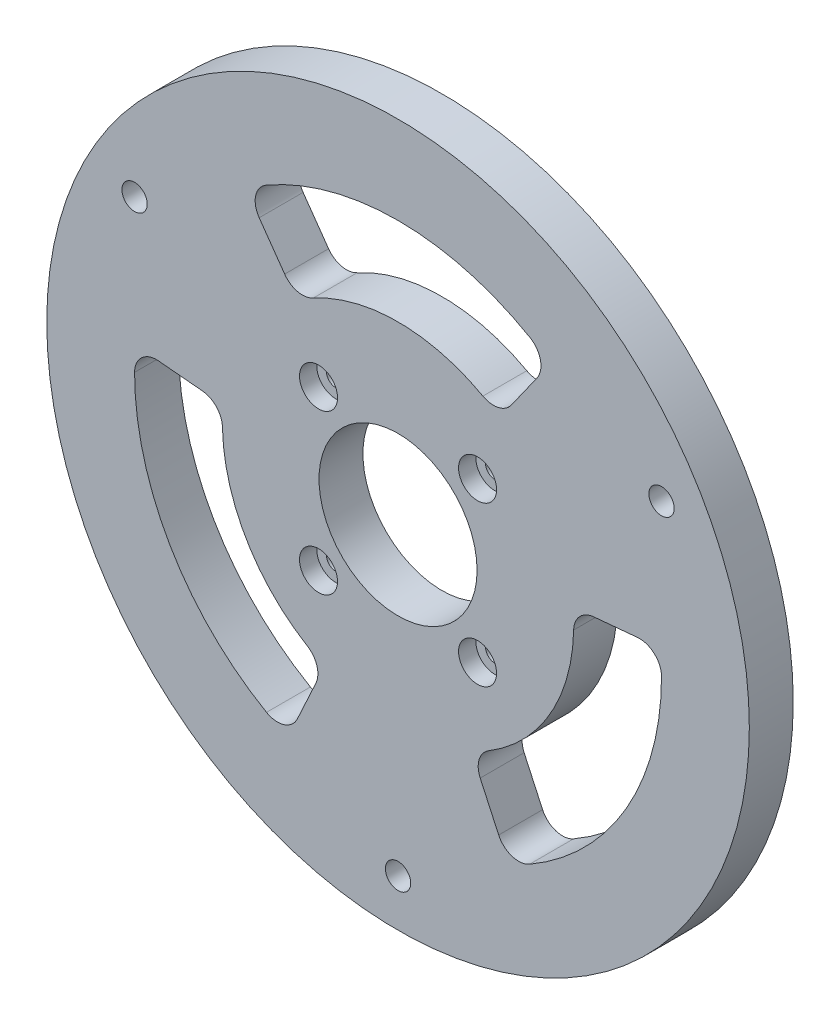
SolidWorks part; units mm, degrees
material "Acrylic (Medium-high impact)"
ref_plane "Front Plane" through (0, 0, 0) normal (0, 0, 1) x (1, 0, 0)
ref_plane "Top Plane" through (0, 0, 0) normal (0, 1, 0) x (1, 0, 0)
ref_plane "Right Plane" through (0, 0, 0) normal (1, 0, 0) x (0, 0, -1)
sketch "Sketch1" plane through (0, 0, 0) normal (0, 0, 1) x (1, 0, 0)
  circle A0 centre (0, 0) radius 50.8
  dimension "D1" = 101.6
extrude "Boss-Extrude1" add sketch "Sketch1" along normal blind 6.35
sketch "Sketch2" plane through (0, 0, 6.35) normal (0, 0, 1) x (1, 0, 0)
  circle A0 centre (0, 0) radius 11.43
  dimension "D1" = 22.86
extrude "Cut-Extrude1" cut sketch "Sketch2" against normal through all
hole_wizard "CBORE for M2.5 SHCS1" positions "Sketch3" profile "Sketch5" counterbore size "M2.5" standard "ANSI Metric"
sketch "Sketch3" plane through (0, 0, 6.35) normal (0, 0, 1) x (1, 0, 0)
  line L1 (-11.5, -11.5) -> (11.5, -11.5)
  line L2 (-11.5, -11.5) -> (-11.5, 11.5)
  line L3 (-11.5, 11.5) -> (11.5, 11.5)
  line L4 (11.5, -11.5) -> (11.5, 11.5)
  line L5 (-11.5, -11.5) -> (11.5, 11.5) construction
  line L6 (-11.5, 11.5) -> (11.5, -11.5) construction
  point P1 (0, 0)
  point P2 (11.5, 11.5)
  point P59 (-11.5, -11.5)
  point P60 (-11.5, 11.5)
  point P61 (11.5, -11.5)
  dimension "D1" = 23
sketch "Sketch5" plane through (0, 0, 6.35) normal (1, 0, 0) x (0, -1, 0)
  line L0 (0, 0) -> (0, 10.9712)
  line L1 (0, 10.9712) -> (1.35, 10.16)
  line L2 (1.35, 10.16) -> (1.35, 2.5)
  line L3 (1.35, 2.5) -> (2.75, 2.5)
  line L4 (2.75, 2.5) -> (2.75, 0)
  line L5 (2.75, 0) -> (0, 0)
  line L10 (0, 10.9712) -> (-1.35, 10.16) construction
  line L11 (0, -6.35) -> (0, 107.95) construction
  dimension "Hole Dia." = 2.7
  dimension "Hole Depth" = 10.16
  dimension "C'Bore Dia." = 5.5
  dimension "C'Bore Depth" = 2.5
  dimension "Drill Angle" = 118
hole_wizard "#6 Clearance Hole1" positions "Sketch7" profile "Sketch9" hole size "#6" standard "ANSI Inch"
sketch "Sketch7" plane through (0, 0, 6.35) normal (0, 0, 1) x (1, 0, 0)
  line L1 (0, -43.9941) -> (38.1, 21.997)
  line L2 (38.1, 21.997) -> (-38.1, 21.997)
  line L3 (-38.1, 21.997) -> (0, -43.9941)
  line L8 (-11.5, 11.5) -> (11.5, 11.5) construction
  circle A0 centre (0, 0) radius 21.997 construction
  point P3 (0, -43.9941)
  point P4 (38.1, 21.997)
  point P5 (-38.1, 21.997)
  dimension "D1" = 76.2
sketch "Sketch9" plane through (-38.1, 21.997, 6.35) normal (1, 0, 0) x (0, -1, 0)
  line L0 (0, 0) -> (0, 11.2589)
  line L1 (0, 11.2589) -> (1.8288, 10.16)
  line L2 (1.8288, 10.16) -> (1.8288, 0)
  line L5 (1.8288, 0) -> (0, 0)
  line L10 (0, 11.2589) -> (-1.8288, 10.16) construction
  line L11 (0, -6.35) -> (0, 107.95) construction
  dimension "Hole Dia." = 3.6576
  dimension "Hole Depth" = 10.16
  dimension "Drill Angle" = 118
fillet "Fillet1" [suppressed] radius 0.508
sketch "Sketch10" plane through (0, 0, 6.35) normal (0, 0, 1) x (1, 0, 0)
  line L0 (0, 0) -> (-21.9974, 31.1083) construction
  line L1 (0, 0) -> (21.9974, 31.1083) construction
  line L2 (14.6649, 20.7388) -> (21.9974, 31.1083)
  line L3 (-14.6649, 20.7388) -> (-21.9974, 31.1083)
  circle A0 centre (0, 0) radius 25.4 construction
  circle A1 centre (0, 0) radius 38.1 construction
  arc A4 (-21.9974, 31.1083) -> (21.9974, 31.1083) centre (0, 0) cw
  arc A5 (-14.6649, 20.7388) -> (14.6649, 20.7388) centre (0, 0) cw
  circle A6 centre (11.5, 11.5) radius 2.75 construction
  circle A7 centre (-11.5, 11.5) radius 2.75 construction
  dimension "D1" = 50.8
  dimension "D2" = 12.7
extrude "Cut-Extrude2" cut sketch "Sketch10" against normal through all
fillet "Fillet2" radius 3.175 4 edges at (-14.6649, 20.7388, 3.175) (14.6649, 20.7388, 3.175) (21.9974, 31.1083, 3.175) (-21.9974, 31.1083, 3.175)
pattern_circular "CirPattern1" count 3 over 360 about axis through (0, 0, 0) along (0, 0, 1) of "Cut-Extrude2", "Fillet2"
